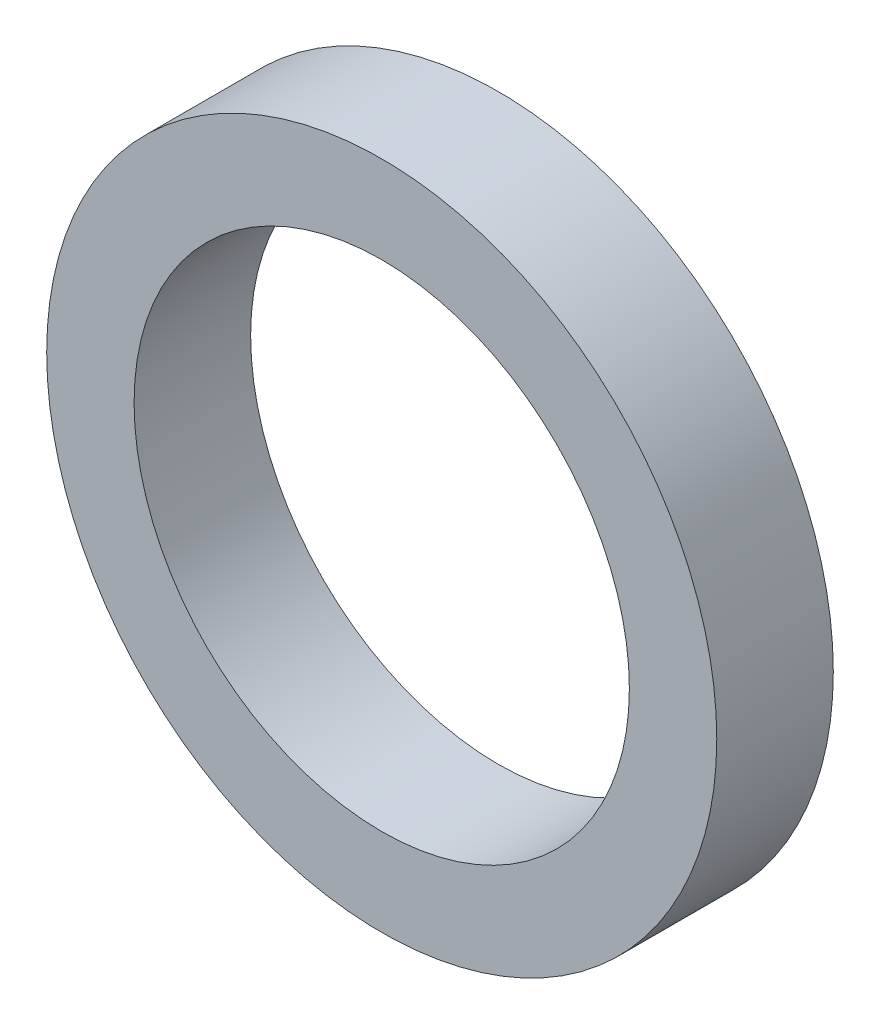
SolidWorks part; units mm, degrees
ref_plane "前视基准面" through (0, 0, 0) normal (0, 0, 1) x (1, 0, 0)
ref_plane "上视基准面" through (0, 0, 0) normal (0, 1, 0) x (1, 0, 0)
ref_plane "右视基准面" through (0, 0, 0) normal (1, 0, 0) x (0, 0, -1)
sketch "草图1" plane through (0, 0, 0) normal (0, 0, 1) x (1, 0, 0)
  circle A0 centre (0, 0) radius 8.5
  circle A1 centre (0, 0) radius 11.5
  dimension "D1" = 17
  dimension "D2" = 23
extrude "凸台-拉伸1" add sketch "草图1" along normal blind 4
